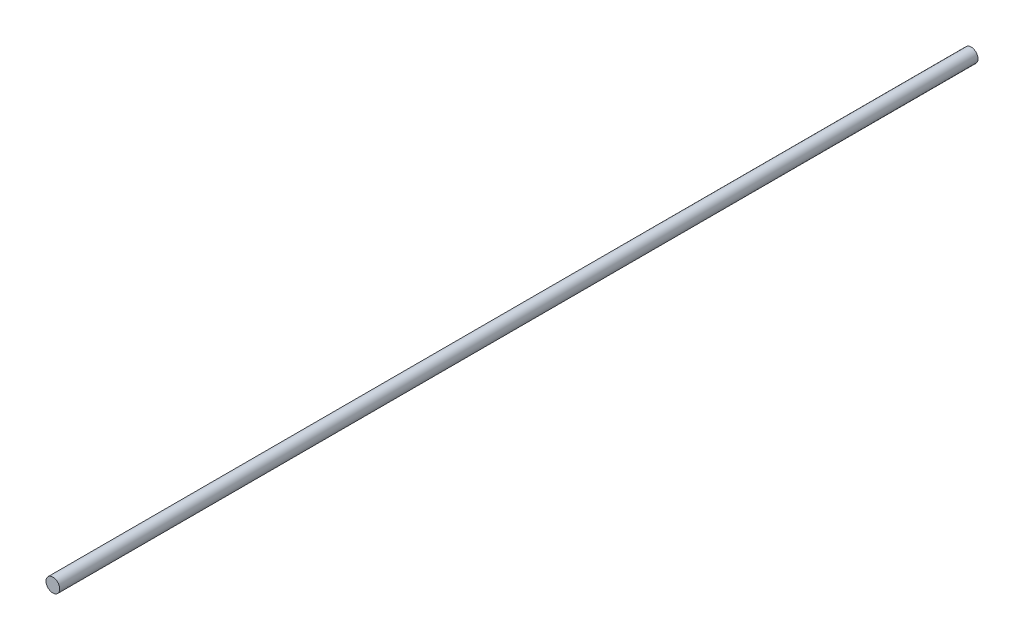
SolidWorks part; units mm, degrees
ref_plane "Front Plane" through (0, 0, 0) normal (0, 0, 1) x (1, 0, 0)
ref_plane "Top Plane" through (0, 0, 0) normal (0, 1, 0) x (1, 0, 0)
ref_plane "Right Plane" through (0, 0, 0) normal (1, 0, 0) x (0, 0, -1)
sketch "Sketch1" plane through (0, 0, 0) normal (0, 0, 1) x (1, 0, 0)
  circle A0 centre (0, 0) radius 0.75
extrude "Boss-Extrude1" add sketch "Sketch1" along normal blind 100
